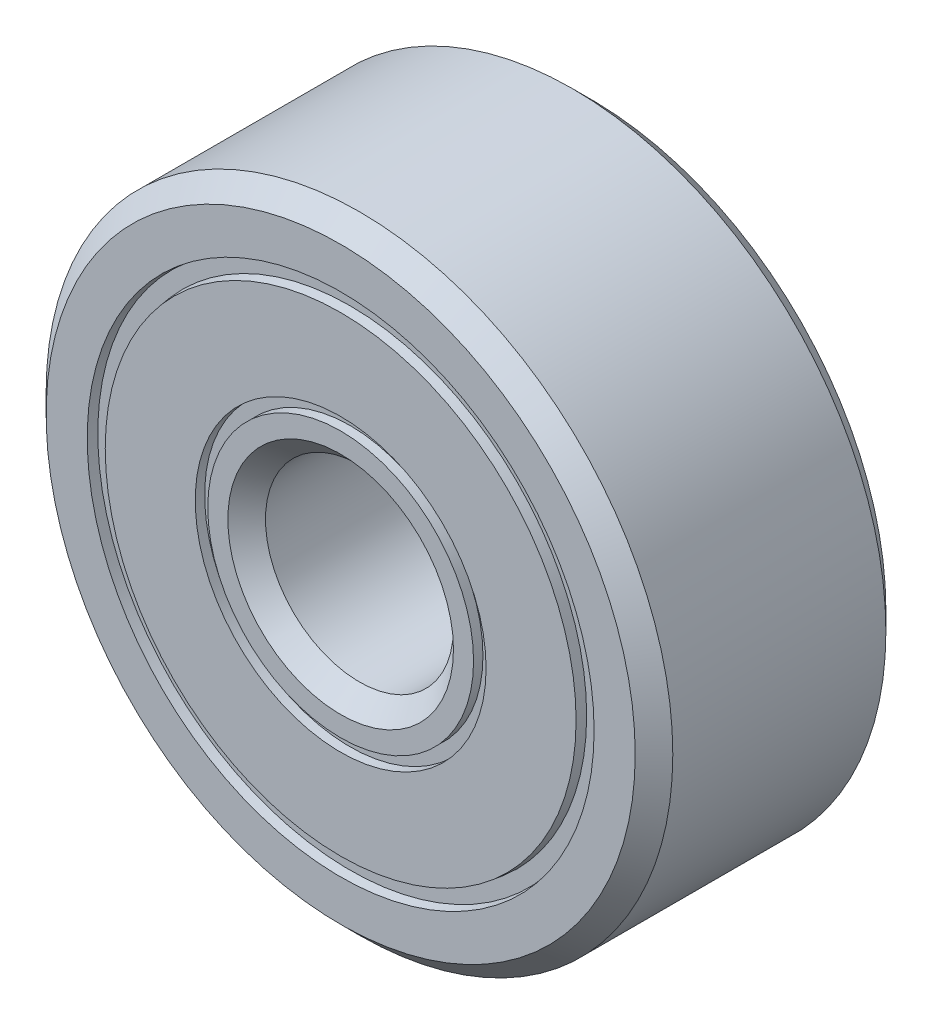
SolidWorks part; units mm, degrees
ref_plane "Alzado" through (0, 0, 0) normal (0, 0, 1) x (1, 0, 0)
ref_plane "Planta" through (0, 0, 0) normal (0, 1, 0) x (1, 0, 0)
ref_plane "Vista lateral" through (0, 0, 0) normal (1, 0, 0) x (0, 0, -1)
sketch "Croquis1" plane through (0, 0, 0) normal (0, 0, 1) x (1, 0, 0)
  circle A0 centre (0, 0) radius 1.5
  circle A1 centre (0, 0) radius 5
  dimension "D1" = 3
  dimension "D2" = 10
extrude "Saliente-Extruir1" add sketch "Croquis1" along normal blind 4
chamfer "Chaflán1" distance 0.3 angle 45 4 edges at (5, 0, 0) (5, 0, 4) (1.5, 0, 4) (1.5, 0, 0)
sketch "Croquis2" plane through (0, 0, 0) normal (1, 0, 0) x (0, 0, -1)
  line L0 (-4.85, 4.1505) -> (-3.85, 4.0255)
  line L1 (-3.85, 4.0255) -> (-3.85, 3.7755)
  line L2 (-3.85, 3.7755) -> (-4.85, 3.6505)
  line L3 (-4.85, 3.6505) -> (-4.85, 4.1505)
  line L4 (-7.1588, 3.9005) -> (-4.5217, 3.9005) construction
  line L5 (-2, 12.5365) -> (-2, -11.2918) construction
  line L6 (-3.7, -5) -> (-3.7, 5) construction
  line L7 (-0.3, 5) -> (-0.3, -5) construction
  line L8 (-4, 4.7) -> (-4, -4.7) construction
  line L9 (0.85, 3.6505) -> (0.85, 4.1505)
  line L10 (-0.15, 3.7755) -> (0.85, 3.6505)
  line L11 (-0.15, 4.0255) -> (-0.15, 3.7755)
  line L12 (0.85, 4.1505) -> (-0.15, 4.0255)
  line L13 (-4.85, 2.3207) -> (-3.85, 2.3207)
  line L14 (-4.85, 2.3207) -> (-4.85, 2.1207)
  line L15 (-4.85, 2.1207) -> (-3.85, 2.1207)
  line L16 (-3.85, 2.3207) -> (-3.85, 2.1207)
  line L17 (-0.15, 2.3207) -> (-0.15, 2.1207)
  line L18 (0.85, 2.1207) -> (-0.15, 2.1207)
  line L19 (0.85, 2.3207) -> (0.85, 2.1207)
  line L20 (0.85, 2.3207) -> (-0.15, 2.3207)
  dimension "D1" = 0.25
  dimension "D2" = 0.5
  dimension "D3" = 0.15
  dimension "D5" = 1
  dimension "D6" = 0.2
sketch "Croquis3" plane through (0, 0, 0) normal (1, 0, 0) x (0, 0, -1)
  line L0 (-12.4113, 0) -> (6.9361, 0) construction
revolve "Cortar-Revolución1" cut sketch "Croquis2" angle 360 about L0
